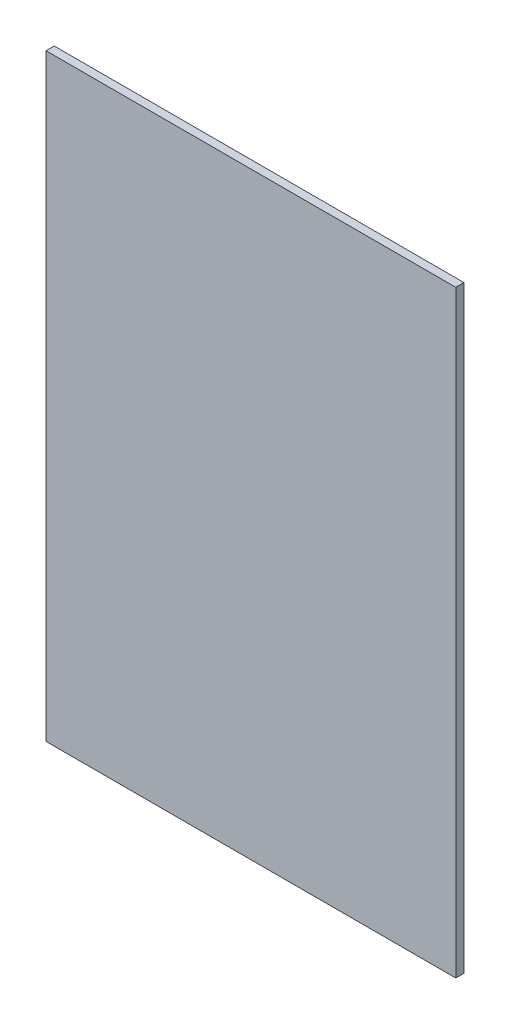
SolidWorks part; units mm, degrees
material "Acrylic (Medium-high impact)"
ref_plane "Front Plane" through (0, 0, 0) normal (0, 0, 1) x (1, 0, 0)
ref_plane "Top Plane" through (0, 0, 0) normal (0, 1, 0) x (1, 0, 0)
ref_plane "Right Plane" through (0, 0, 0) normal (1, 0, 0) x (0, 0, -1)
sketch "Sketch1" plane through (0, 0, 0) normal (0, 0, 1) x (1, 0, 0)
  line L1 (0, 0) -> (317.5, 0)
  line L2 (0, 0) -> (0, 463.55)
  line L3 (0, 463.55) -> (317.5, 463.55)
  line L4 (317.5, 0) -> (317.5, 463.55)
  dimension "D1" = 317.5
  dimension "D2" = 463.55
extrude "Boss-Extrude1" add sketch "Sketch1" along normal blind 6.35
